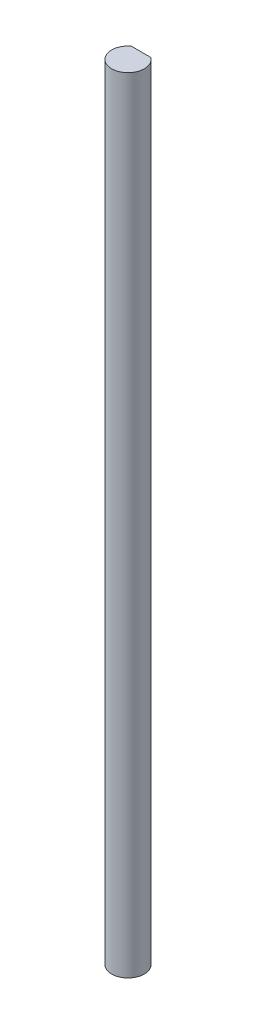
SolidWorks part; units mm, degrees
ref_plane "Front Plane" through (0, 0, 0) normal (0, 0, 1) x (1, 0, 0)
ref_plane "Top Plane" through (0, 0, 0) normal (0, 1, 0) x (1, 0, 0)
ref_plane "Right Plane" through (0, 0, 0) normal (1, 0, 0) x (0, 0, -1)
sketch "Sketch1" plane through (0, 0, 0) normal (0, 1, 0) x (1, 0, 0)
  line L0 (-1.905, 2.54) -> (1.905, 2.54)
  arc A0 (-1.905, 2.54) -> (1.905, 2.54) centre (0, 0) ccw
  dimension "D1" = 6.35
  dimension "D2" = 2.54
extrude "Boss-Extrude1" add sketch "Sketch1" along normal blind 152.4
